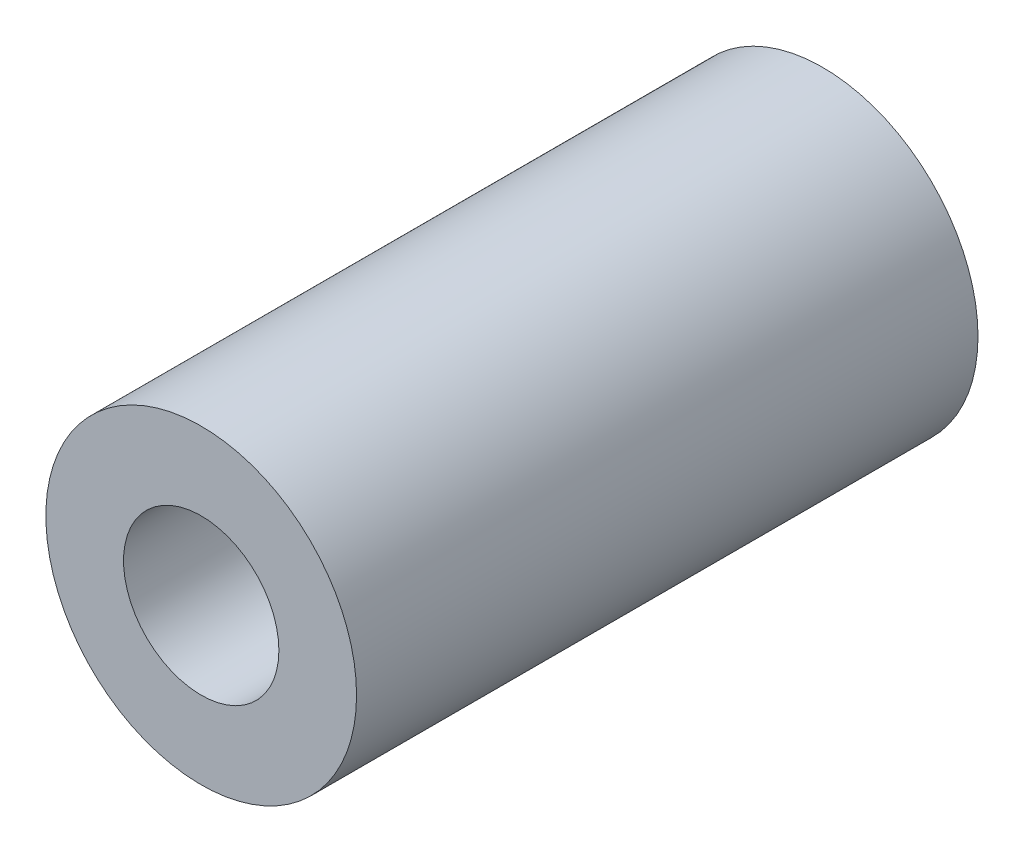
SolidWorks part; units mm, degrees
ref_plane "Front Plane" through (0, 0, 0) normal (0, 0, 1) x (1, 0, 0)
ref_plane "Top Plane" through (0, 0, 0) normal (0, 1, 0) x (1, 0, 0)
ref_plane "Right Plane" through (0, 0, 0) normal (1, 0, 0) x (0, 0, -1)
sketch "Sketch1" plane through (0, 0, 0) normal (0, 0, 1) x (1, 0, 0)
  circle A0 centre (0, 0) radius 5
  circle A1 centre (0, 0) radius 2.5
extrude "Boss-Extrude1" add sketch "Sketch1" along normal blind 20
sketch "Sketch2" plane through (0, 0, 0) normal (0, 1, 0) x (1, 0, 0)
  line L0 (0, 0) -> (0.1315, -20) construction
  line L1 (-5, -20) -> (5, -20) construction
  circle A0 centre (0.0329, -5) radius 1.5
  circle A1 centre (0.0986, -15) radius 1.5
  dimension "D1" = 3
  dimension "D2" = 3
  dimension "D3" = 5
  dimension "D4" = 5
extrude "Cut-Extrude1" cut sketch "Sketch2" against normal blind 10
